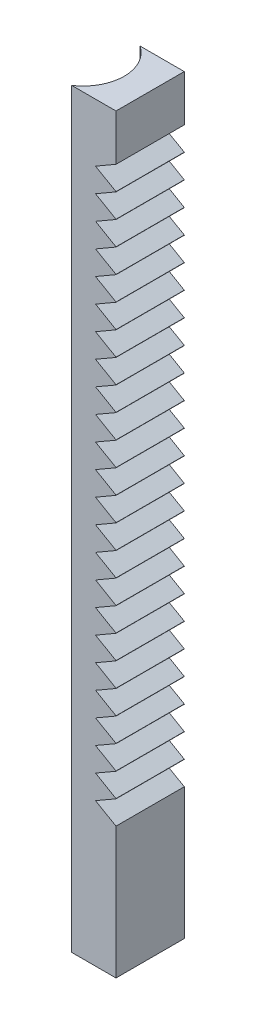
SolidWorks part; units mm, degrees
ref_plane "Front Plane" through (0, 0, 0) normal (0, 0, 1) x (1, 0, 0)
ref_plane "Top Plane" through (0, 0, 0) normal (0, 1, 0) x (1, 0, 0)
ref_plane "Right Plane" through (0, 0, 0) normal (1, 0, 0) x (0, 0, -1)
sketch "Sketch1" plane through (0, 0, 0) normal (0, 1, 0) x (1, 0, 0)
  line L1 (43.3013, -25) -> (69, -25)
  line L3 (43.3013, 25) -> (69, 25)
  line L4 (69, -25) -> (69, 25)
  line L5 (50, 0) -> (69, 25) construction
  line L6 (50, 0) -> (69, -25) construction
  arc A0 (43.3013, -25) -> (43.3013, 25) centre (0, 0) ccw
  point P3 (50, 0)
  dimension "D1" = 100
  dimension "D2" = 50
extrude "Boss-Extrude1" add sketch "Sketch1" along normal blind 550
sketch "Sketch2" plane through (0, 0, 25) normal (0, 0, 1) x (1, 0, 0)
  line L0 (69, 550) -> (69, 0) construction
  line L5 (54, 489.9932) -> (76.5, 477.0028)
  line L6 (54, 507.4932) -> (76.5, 494.5028)
  line L7 (69, 515) -> (69, 514.9932)
  line L8 (76.5, 494.5028) -> (76.5, 520.4836)
  line L9 (76.5, 520.4836) -> (54, 507.4932)
  line L10 (76.5, 477.0028) -> (76.5, 502.9836)
  line L11 (76.5, 502.9836) -> (54, 489.9932)
  line L12 (54, 472.4932) -> (76.5, 459.5028)
  line L13 (76.5, 459.5028) -> (76.5, 485.4836)
  line L14 (76.5, 485.4836) -> (54, 472.4932)
  line L15 (54, 454.9932) -> (76.5, 442.0028)
  line L16 (76.5, 442.0028) -> (76.5, 467.9836)
  line L17 (76.5, 467.9836) -> (54, 454.9932)
  line L18 (54, 437.4932) -> (76.5, 424.5028)
  line L19 (76.5, 424.5028) -> (76.5, 450.4836)
  line L20 (76.5, 450.4836) -> (54, 437.4932)
  line L21 (54, 419.9932) -> (76.5, 407.0028)
  line L22 (76.5, 407.0028) -> (76.5, 432.9836)
  line L23 (76.5, 432.9836) -> (54, 419.9932)
  line L24 (54, 402.4932) -> (76.5, 389.5028)
  line L25 (76.5, 389.5028) -> (76.5, 415.4836)
  line L26 (76.5, 415.4836) -> (54, 402.4932)
  line L27 (54, 384.9932) -> (76.5, 372.0028)
  line L28 (76.5, 372.0028) -> (76.5, 397.9836)
  line L29 (76.5, 397.9836) -> (54, 384.9932)
  line L30 (54, 367.4932) -> (76.5, 354.5028)
  line L31 (76.5, 354.5028) -> (76.5, 380.4836)
  line L32 (76.5, 380.4836) -> (54, 367.4932)
  line L33 (54, 349.9932) -> (76.5, 337.0028)
  line L34 (76.5, 337.0028) -> (76.5, 362.9836)
  line L35 (76.5, 362.9836) -> (54, 349.9932)
  line L36 (54, 332.4932) -> (76.5, 319.5028)
  line L37 (76.5, 319.5028) -> (76.5, 345.4836)
  line L38 (76.5, 345.4836) -> (54, 332.4932)
  line L39 (54, 314.9932) -> (76.5, 302.0028)
  line L40 (76.5, 302.0028) -> (76.5, 327.9836)
  line L41 (76.5, 327.9836) -> (54, 314.9932)
  line L42 (54, 297.4932) -> (76.5, 284.5028)
  line L43 (76.5, 284.5028) -> (76.5, 310.4836)
  line L44 (76.5, 310.4836) -> (54, 297.4932)
  line L45 (54, 279.9932) -> (76.5, 267.0028)
  line L46 (76.5, 267.0028) -> (76.5, 292.9836)
  line L47 (76.5, 292.9836) -> (54, 279.9932)
  line L48 (54, 262.4932) -> (76.5, 249.5028)
  line L49 (76.5, 249.5028) -> (76.5, 275.4836)
  line L50 (76.5, 275.4836) -> (54, 262.4932)
  line L51 (54, 244.9932) -> (76.5, 232.0028)
  line L52 (76.5, 232.0028) -> (76.5, 257.9836)
  line L53 (76.5, 257.9836) -> (54, 244.9932)
  line L54 (54, 227.4932) -> (76.5, 214.5028)
  line L55 (76.5, 214.5028) -> (76.5, 240.4836)
  line L56 (76.5, 240.4836) -> (54, 227.4932)
  line L57 (54, 209.9932) -> (76.5, 197.0028)
  line L58 (76.5, 197.0028) -> (76.5, 222.9836)
  line L59 (76.5, 222.9836) -> (54, 209.9932)
  line L60 (54, 192.4932) -> (76.5, 179.5028)
  line L61 (76.5, 179.5028) -> (76.5, 205.4836)
  line L62 (76.5, 205.4836) -> (54, 192.4932)
  line L63 (54, 174.9932) -> (76.5, 162.0028)
  line L64 (76.5, 162.0028) -> (76.5, 187.9836)
  line L65 (76.5, 187.9836) -> (54, 174.9932)
  line L66 (54, 157.4932) -> (76.5, 144.5028)
  line L67 (76.5, 144.5028) -> (76.5, 170.4836)
  line L68 (76.5, 170.4836) -> (54, 157.4932)
  line L69 (54, 139.9932) -> (76.5, 127.0028)
  line L70 (76.5, 127.0028) -> (76.5, 152.9836)
  line L71 (76.5, 152.9836) -> (54, 139.9932)
  line L72 (54, 122.4932) -> (76.5, 109.5028)
  line L73 (76.5, 109.5028) -> (76.5, 135.4836)
  line L74 (76.5, 135.4836) -> (54, 122.4932)
  line L75 (54, 104.9932) -> (76.5, 92.0028)
  line L76 (76.5, 92.0028) -> (76.5, 117.9836)
  line L77 (76.5, 117.9836) -> (54, 104.9932)
  circle A0 centre (69, 507.4932) radius 7.5 construction
  point P0 (69, 275)
  dimension "D1" = 24
extrude "Cut-Extrude1" cut sketch "Sketch2" against normal blind 73 contours L11 L9 L6 | L11 L5 | L11 L14 L12 | L11 L17 L15 | L11 L20 L18 | L11 L23 L21 | L11 L26 L24 | L11 L29 L27 | L11 L32 L30 | L11 L35 L33 | L11 L38 L36 | L11 L41 L39 | L11 L44 L42 | L11 L47 L45 | L11 L50 L48 | L11 L53 L51 | L11 L56 L54 | L11 L59 L57 | L11 L62 L60 | L11 L77 L75 | L11 L74 L72 | L11 L71 L69 | L11 L68 L66 | L11 L65 L63
sketch "Sketch3" plane through (0, 550, 0) normal (0, 1, 0) x (1, 0, 0)
  line L0 (69, -25) -> (69, 25) construction
  line L5 (43.3013, 25) -> (36.5831, 25)
  line L6 (43.3013, -25) -> (36.5831, -25)
  arc A0 (43.3013, -25) -> (43.3013, 25) centre (0, 0) ccw construction
  arc A1 (36.5831, -25) -> (36.5831, 25) centre (20, 0) ccw
  arc A2 (43.3013, 25) -> (50, 0) centre (0, 0) cw
  arc A3 (50, 0) -> (43.3013, -25) centre (0, 0) cw
  point P0 (69, 0)
  arc M9 (43.3013, 25) -> (43.3013, -25) centre (0, 0) cw
  dimension "D1" = 30
extrude "Boss-Extrude2" add sketch "Sketch3" against normal up to surface (550 mm away) contours A1 L6 M9 | A1 L5 M9 up to face at (57.8253, 0, 0)
sketch "Sketch4" plane through (0, 550, 0) normal (0, 1, 0) x (1, 0, 0)
  point P0 (36.5831, 0)
